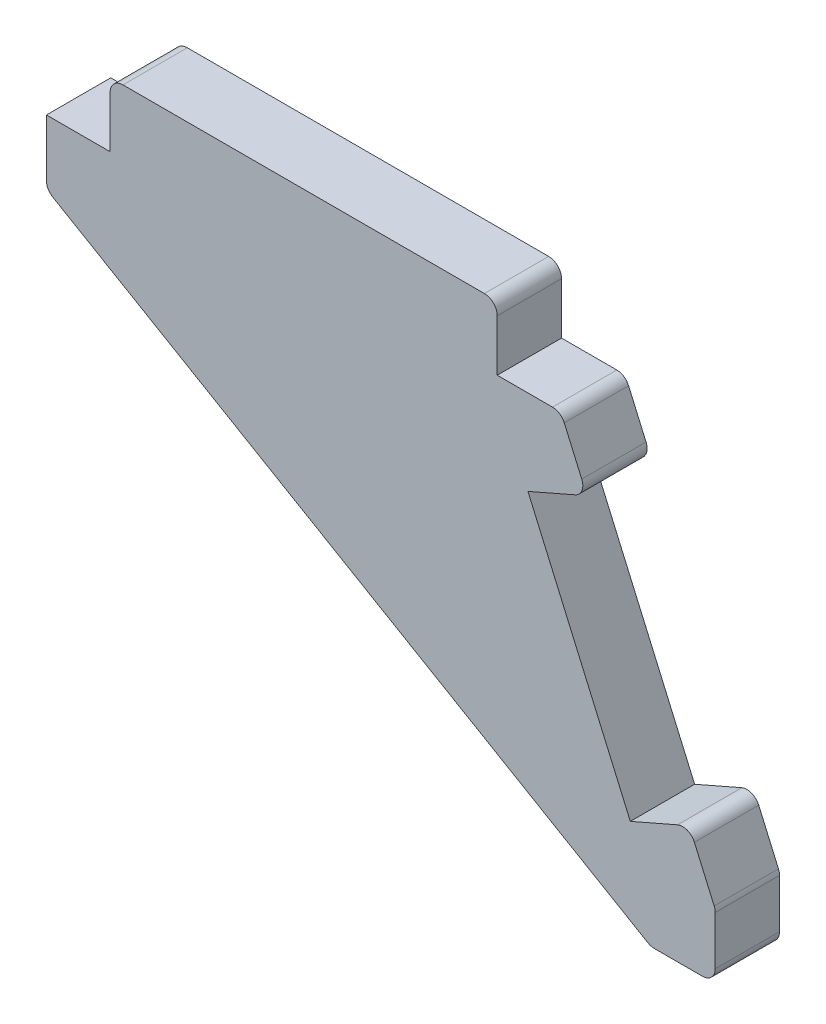
SolidWorks part; units mm, degrees
ref_plane "Front" through (0, 0, 0) normal (0, 0, 1) x (1, 0, 0)
ref_plane "Top" through (0, 0, 0) normal (0, 1, 0) x (1, 0, 0)
ref_plane "Right" through (0, 0, 0) normal (1, 0, 0) x (0, 0, -1)
sketch "Sketch1" plane through (0, 0, 0) normal (0, 0, 1) x (1, 0, 0)
  line L0 (4.95, 5) -> (40, 5) construction
  line L1 (4.95, 5) -> (4.95, 0) construction
  line L2 (35.05, 0) -> (40, 0) construction
  line L3 (40, 5) -> (40, 0) construction
  line L4 (40, 0) -> (42.02, -4.6284) construction
  line L5 (52, -27.4955) -> (47.4174, -29.4955) construction
  line L6 (47.4174, -29.4955) -> (35.4174, -2) construction
  line L7 (35.4174, -2) -> (40, 0) construction
  line L8 (42.02, -4.6284) -> (37.4374, -6.6284)
  line L9 (37.4374, -6.6284) -> (45.3974, -24.8671)
  line L10 (45.3974, -24.8671) -> (49.98, -22.8671)
  line L12 (35.05, 5) -> (4.95, 5)
  line L13 (35.05, 5) -> (35.05, 0)
  line L15 (4.95, 5) -> (4.95, 0)
  line L16 (49.98, -22.8671) -> (52, -27.4955) construction
  line L17 (49.98, -22.8671) -> (52, -27.4955)
  line L18 (52, -27.4955) -> (52, -32.4955)
  line L19 (42.02, -4.6284) -> (40, 0)
  line L20 (40, 0) -> (35.05, 0)
  line L21 (4.95, 0) -> (0, 0)
  line L22 (0, 0) -> (0, -5)
  line L23 (0, -5) -> (47, -32.4955)
  line L24 (47, -32.4955) -> (52, -32.4955)
  dimension "D1" = 30
  dimension "D2" = 5.05
  dimension "D3" = 4.95
  dimension "D4" = 5
  dimension "D5" = 5
  dimension "D6" = 5
  dimension "D7" = 4.95
  dimension "D8" = 19.9
extrude "Boss-Extrude1" add sketch "Sketch1" along normal blind 5
fillet "Fillet1" radius 1 9 edges at (40, 0, 2.5) (0, -5, 2.5) (52, -27.4955, 2.5) (52, -32.4955, 2.5) (47, -32.4955, 2.5) (49.98, -22.8671, 2.5) (42.02, -4.6284, 2.5) (35.05, 5, 2.5) (4.95, 5, 2.5)
